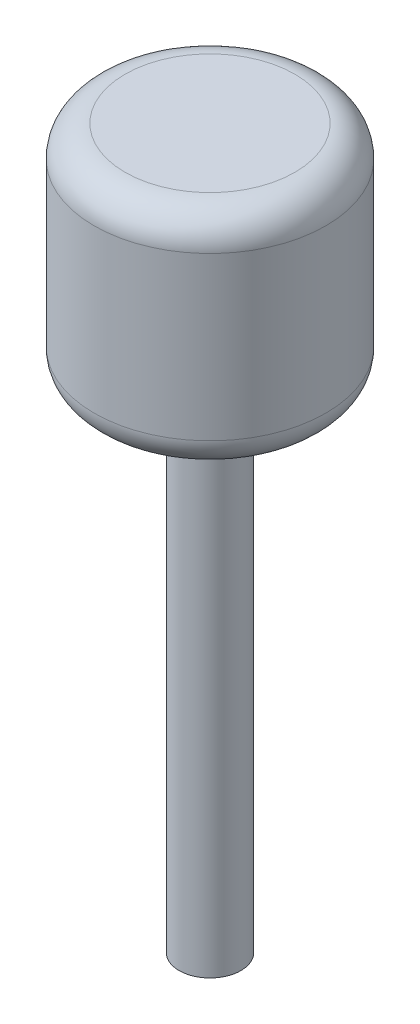
SolidWorks part; units mm, degrees
ref_plane "前视基准面" through (0, 0, 0) normal (0, 0, 1) x (1, 0, 0)
ref_plane "上视基准面" through (0, 0, 0) normal (0, 1, 0) x (1, 0, 0)
ref_plane "右视基准面" through (0, 0, 0) normal (1, 0, 0) x (0, 0, -1)
sketch "草图1" plane through (0, 0, 0) normal (0, 1, 0) x (1, 0, 0)
  circle A0 centre (0, 0) radius 2
extrude "凸台-拉伸1" add sketch "草图1" along normal blind 30
sketch "草图2" plane through (0, 30, 0) normal (0, 1, 0) x (1, 0, 0)
  circle A0 centre (0, 0) radius 3
extrude "凸台-拉伸2" add sketch "草图2" along normal blind 2
sketch "草图3" plane through (0, 32, 0) normal (0, 1, 0) x (1, 0, 0)
  circle A0 centre (0, 0) radius 7.5
extrude "凸台-拉伸3" add sketch "草图3" along normal blind 14.5
fillet "圆角1" radius 2 2 edges at (0, 32, 7.5) (0, 46.5, 7.5)
fillet "圆角2" radius 0.5 2 edges at (0, 30, 3) (0, 32, 3)
